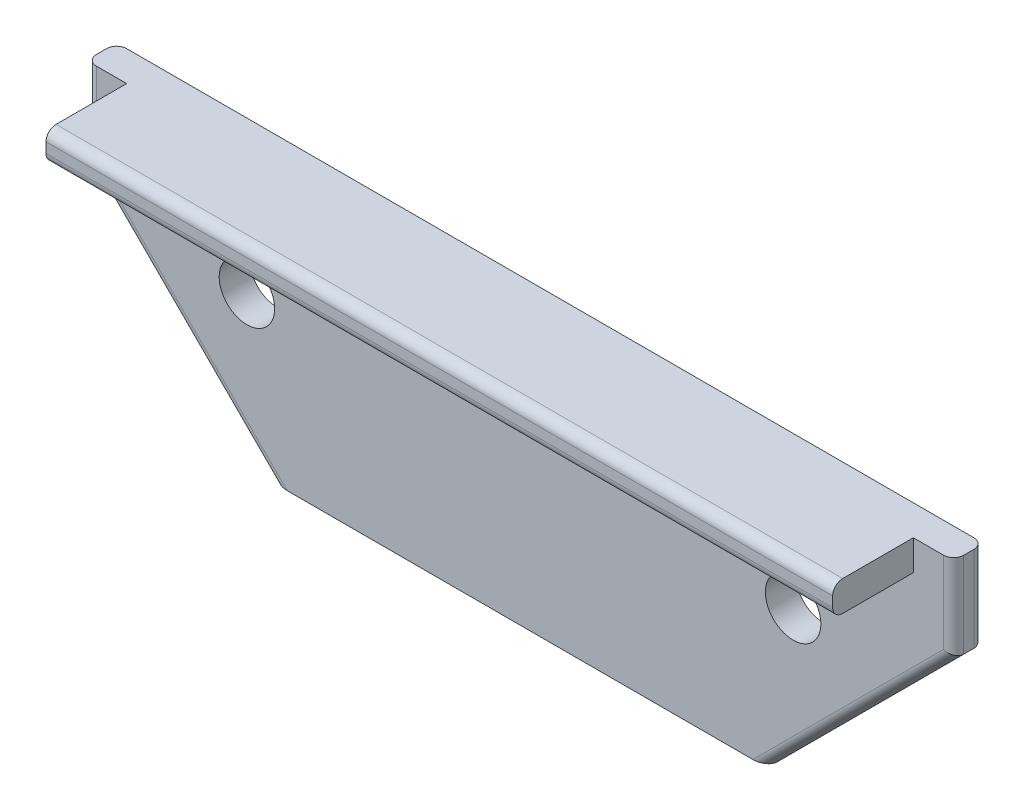
SolidWorks part; units mm, degrees
material "6061 Alloy"
ref_plane "Front Plane" through (0, 0, 0) normal (0, 0, 1) x (1, 0, 0)
ref_plane "Top Plane" through (0, 0, 0) normal (0, 1, 0) x (1, 0, 0)
ref_plane "Right Plane" through (0, 0, 0) normal (1, 0, 0) x (0, 0, -1)
ref_plane "Plane1" through (0, 0, -7.9375) normal (0, 0, 1) x (1, 0, 0)
sketch "Sketch1" plane through (0, 0, -7.9375) normal (0, 0, 1) x (1, 0, 0)
  line L0 (136.525, 15.875) -> (136.525, 42.8625)
  line L1 (136.525, 42.8625) -> (-136.525, 42.8625)
  line L2 (-136.525, 42.8625) -> (-136.525, 15.875)
  line L3 (-136.525, 15.875) -> (-77.7875, -42.8625)
  line L4 (-77.7875, -42.8625) -> (77.7875, -42.8625)
  line L5 (77.7875, -42.8625) -> (136.525, 15.875)
extrude "Boss-Extrude1" add sketch "Sketch1" against normal blind 9.525
sketch "Sketch2" plane through (0, 0, -7.9375) normal (0, 0, 1) x (1, 0, 0)
  line L0 (-123.825, 33.3375) -> (-123.825, 42.8625)
  line L1 (-123.825, 42.8625) -> (123.825, 42.8625)
  line L2 (123.825, 42.8625) -> (123.825, 33.3375)
  line L3 (123.825, 33.3375) -> (-123.825, 33.3375)
extrude "Boss-Extrude2" add sketch "Sketch2" along normal blind 25.4
hole_wizard "M16 Clearance Hole1" positions "Sketch4" profile "Sketch3" hole size "M16" standard "ANSI Metric"
sketch "Sketch4" plane through (0, 0, -17.4625) normal (0, 0, -1) x (-1, 0, 0)
  point P0 (-85.979, 4.7625)
  point P1 (85.979, 4.7625)
sketch "Sketch3" plane through (85.979, 4.7625, -17.4625) normal (1, 0, 0) x (0, 1, 0)
  line L0 (0, 0) -> (0, 34.925)
  line L1 (0, 34.925) -> (8.7312, 34.925)
  line L2 (8.7312, 34.925) -> (8.7312, 0)
  line L5 (8.7312, 0) -> (0, 0)
  line L11 (0, -6.35) -> (0, 107.95) construction
  dimension "Thru Hole Dia." = 17.4625
  dimension "Thru Hole Depth" = 34.925
fillet "Fillet1" radius 3.175 10 edges at (-107.1562, -13.4937, -17.4625) (-136.525, 29.3687, -17.4625) (-136.525, 29.3687, -7.9375) (-107.1562, -13.4937, -7.9375) (136.525, 29.3687, -17.4625) (107.1562, -13.4937, -17.4625) (0, 42.8625, 17.4625) (107.1562, -13.4937, -7.9375) (136.525, 29.3687, -7.9375) (0, 33.3375, 17.4625)
